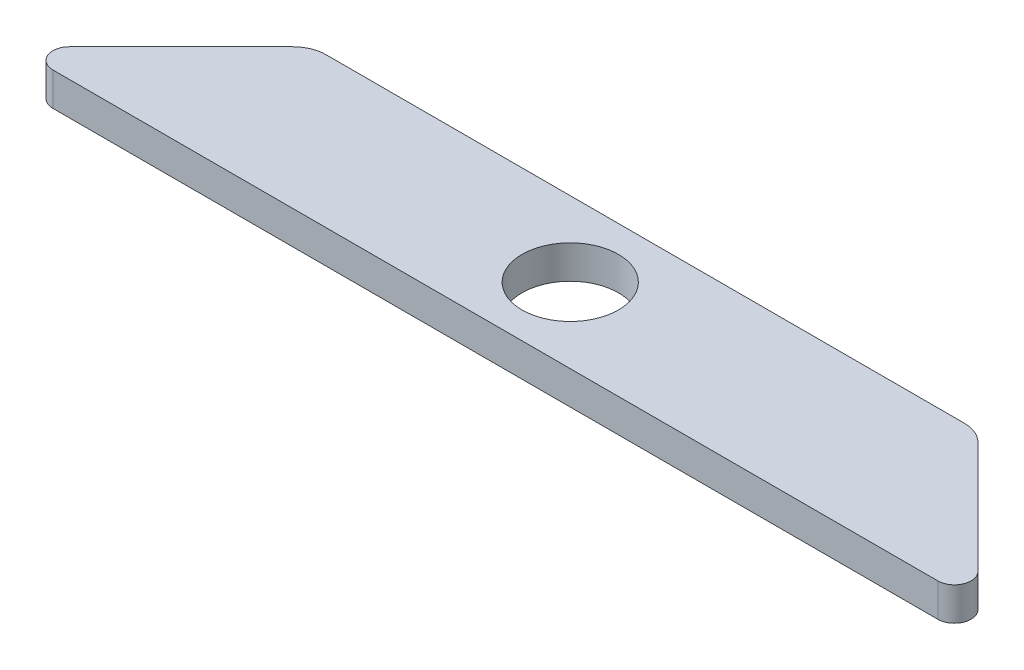
SolidWorks part; units mm, degrees
material "NEOPRENE"
ref_plane "Front Plane" through (0, 0, 0) normal (0, 0, 1) x (1, 0, 0)
ref_plane "Top Plane" through (0, 0, 0) normal (0, 1, 0) x (1, 0, 0)
ref_plane "Right Plane" through (0, 0, 0) normal (1, 0, 0) x (0, 0, -1)
sketch "Sketch1" plane through (0, 0, 0) normal (0, 1, 0) x (1, 0, 0)
  line L0 (-13.2929, -2.5303) -> (13.2929, -2.5303)
  line L1 (13.6464, -1.6768) -> (10.2929, 1.6768)
  line L2 (9.5858, 1.9697) -> (-9.5858, 1.9697)
  line L3 (-10.2929, 1.6768) -> (-13.6464, -1.6768)
  arc A0 (10.2929, 1.6768) -> (9.5858, 1.9697) centre (9.5858, 0.9697) ccw
  arc A1 (-9.5858, 1.9697) -> (-10.2929, 1.6768) centre (-9.5858, 0.9697) ccw
  arc A2 (13.2929, -2.5303) -> (13.6464, -1.6768) centre (13.2929, -2.0303) ccw
  arc A3 (-13.2929, -2.5303) -> (-13.6464, -1.6768) centre (-13.2929, -2.0303) cw
  point P2 (0, 1.9697)
  point P5 (-11.9697, 0)
  point P9 (10, 1.9697)
  point P12 (-10, 1.9697)
  dimension "D4" = 1
  dimension "D5" = 0.5
  dimension "D1" = 45
  dimension "D2" = 20
  dimension "D3" = 4.5
extrude "Boss-Extrude1" add sketch "Sketch1" along normal mid plane 1
sketch "Sketch2" plane through (0, 0.5, 0) normal (0, 1, 0) x (1, 0, 0)
  line L0 (9.5858, 1.9697) -> (-9.5858, 1.9697) construction
  circle A0 centre (0, -0.2803) radius 1.4478
  dimension "D1" = 2.25
  dimension "D2" = 2.8956
extrude "Cut-Extrude1" cut sketch "Sketch2" against normal up to next
